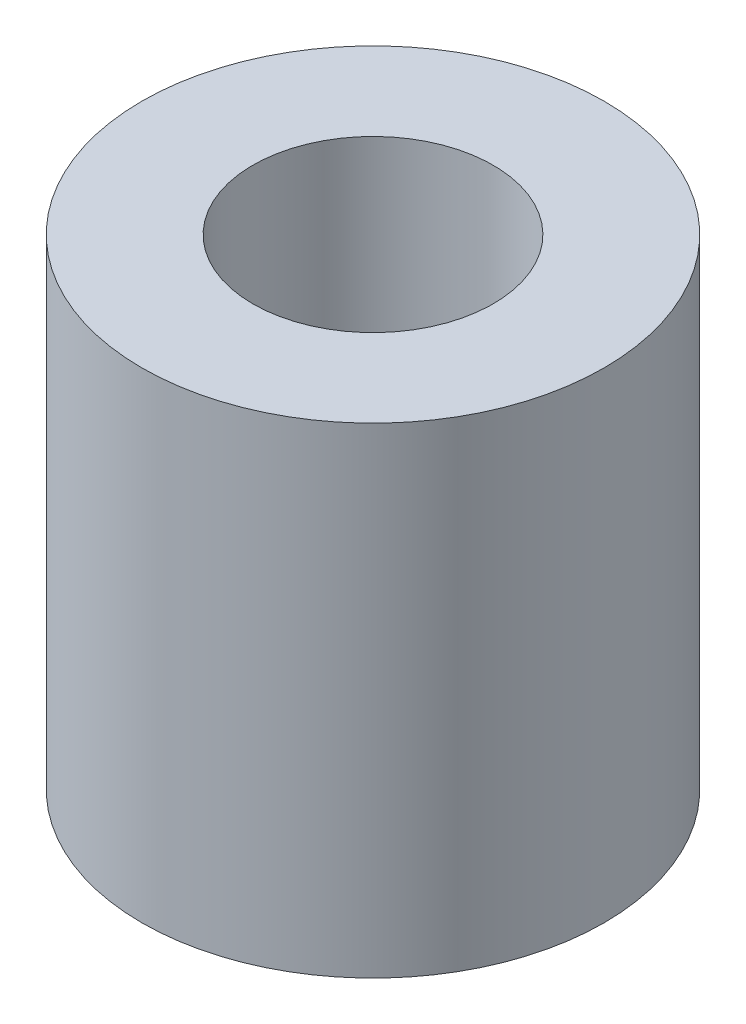
SolidWorks part; units mm, degrees
ref_plane "Face" through (0, 0, 0) normal (0, 0, 1) x (1, 0, 0)
ref_plane "Dessus" through (0, 0, 0) normal (0, 1, 0) x (1, 0, 0)
ref_plane "Droite" through (0, 0, 0) normal (1, 0, 0) x (0, 0, -1)
sketch "Esquisse1" plane through (0, 0, 0) normal (0, 1, 0) x (1, 0, 0)
  circle A0 centre (0, 0) radius 12.5
  circle A1 centre (0, 0) radius 6.5
  dimension "D1" = 25
  dimension "D2" = 13
extrude "Extrusion1" add sketch "Esquisse1" along normal blind 26
